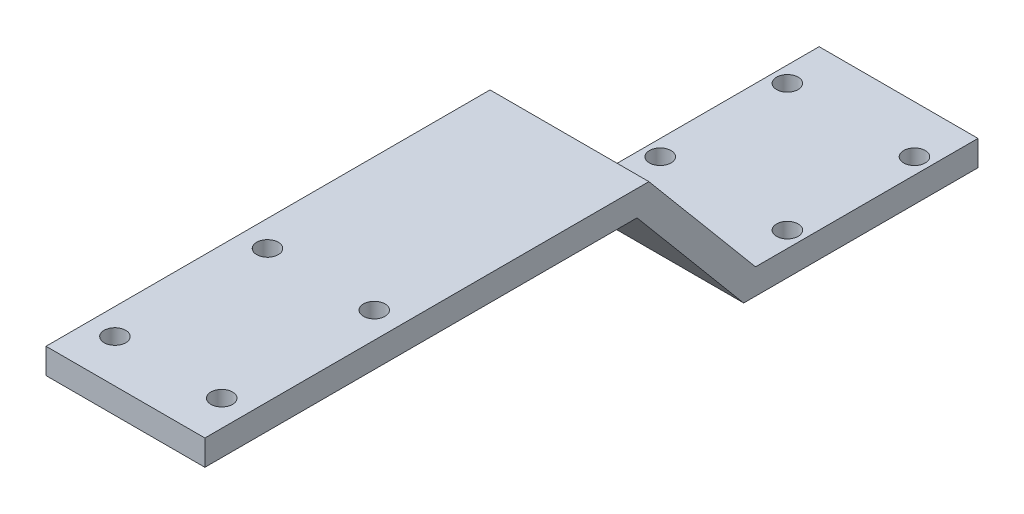
SolidWorks part; units mm, degrees
ref_plane "Front Plane" through (0, 0, 0) normal (0, 0, 1) x (1, 0, 0)
ref_plane "Top Plane" through (0, 0, 0) normal (0, 1, 0) x (1, 0, 0)
ref_plane "Right Plane" through (0, 0, 0) normal (1, 0, 0) x (0, 0, -1)
sketch "Sketch2" plane through (0, 0, 0) normal (1, 0, 0) x (0, 0, -1)
  line L0 (0, 0) -> (0, 4)
  line L1 (0, 4) -> (-35, 4)
  line L2 (-35, 4) -> (-51.782, 24)
  line L3 (-51.782, 24) -> (-121.6472, 24)
  line L4 (0, 0) -> (-36.8652, 0)
  line L5 (-121.6472, 24) -> (-121.6472, 20)
  line L6 (-36.8652, 0) -> (-53.6472, 20)
  line L7 (-53.6472, 20) -> (-121.6472, 20)
  line L8 (-4, 0) -> (-4, 0) construction
  line L9 (-4, 0) -> (-36.8652, 0) construction
  dimension "D2" = 68
  dimension "D3" = 20
  dimension "D4" = 130
  dimension "D5" = 35
  dimension "D1" = 4
extrude "Boss-Extrude1" add sketch "Sketch2" along normal mid plane 25
hole_wizard "M3 Clearance Hole1" positions "Sketch5" profile "Sketch6" hole size "M3" standard "ANSI Metric"
sketch "Sketch5" plane through (0, 24, 0) normal (0, 1, 0) x (1, 0, 0)
  line L0 (0, -127.4881) -> (0, -27.1774) construction
  line L3 (12.5, -121.6472) -> (-12.5, -121.6472) construction
  point P4 (-8.4, -90.8972)
  point P6 (-8.4, -114.8972)
  point P17 (8.4, -114.8972)
  point P18 (8.4, -90.8972)
  point P25 (0, 0)
  point P26 (0, 0)
  point P27 (0, 0)
  point P28 (0, 0)
  dimension "D1" = 6.75
  dimension "D2" = 30.75
  dimension "D3" = 8.4
sketch "Sketch6" plane through (-8.4, 24, 90.8972) normal (1, 0, 0) x (0, 0, 1)
  line L0 (0, 0) -> (0, 9.5215)
  line L1 (0, 9.5215) -> (1.7, 8.5)
  line L2 (1.7, 8.5) -> (1.7, 0)
  line L5 (1.7, 0) -> (0, 0)
  line L10 (0, 9.5215) -> (-1.7, 8.5) construction
  line L11 (0, -6.35) -> (0, 107.95) construction
  dimension "Hole Dia." = 3.4
  dimension "Hole Depth" = 8.5
  dimension "Drill Angle" = 118
hole_wizard "M3 Clearance Hole2" positions "Sketch7" profile "Sketch8" hole size "M3" standard "ANSI Metric"
sketch "Sketch7" plane through (0, 4, 0) normal (0, 1, 0) x (1, 0, 0)
  line L0 (0, 6.97) -> (0, -46.1018) construction
  line L2 (-12.5, -17.5) -> (52.4815, -17.5) construction
  line L3 (-12.5, 0) -> (-12.5, -35) construction
  point P0 (-10, -27.5)
  point P2 (10, -27.5)
  point P4 (10, -7.5)
  point P6 (-10, -7.5)
  dimension "D1" = 10
  dimension "D2" = 10
  dimension "D3" = 10
  dimension "D4" = 10
sketch "Sketch8" plane through (-10, 4, 27.5) normal (1, 0, 0) x (0, 0, 1)
  line L0 (0, 0) -> (0, 9.5215)
  line L1 (0, 9.5215) -> (1.7, 8.5)
  line L2 (1.7, 8.5) -> (1.7, 0)
  line L5 (1.7, 0) -> (0, 0)
  line L10 (0, 9.5215) -> (-1.7, 8.5) construction
  line L11 (0, -6.35) -> (0, 107.95) construction
  dimension "Hole Dia." = 3.4
  dimension "Hole Depth" = 8.5
  dimension "Drill Angle" = 118
